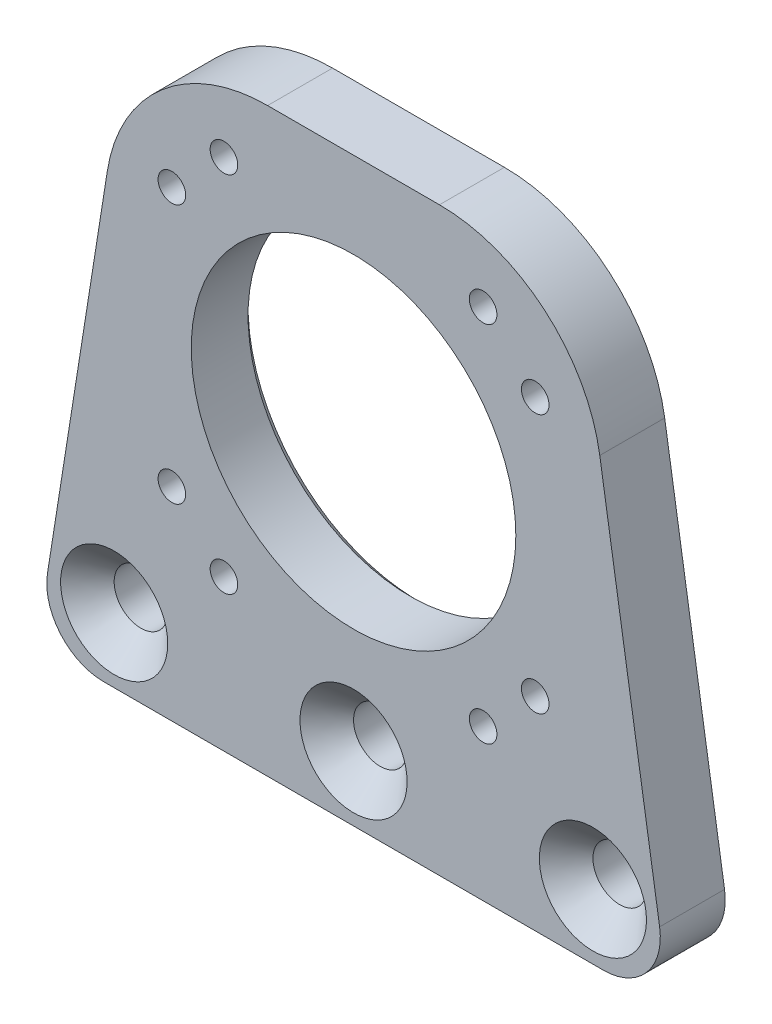
SolidWorks part; units mm, degrees
ref_plane "前视基准面" through (0, 0, 0) normal (0, 0, 1) x (1, 0, 0)
ref_plane "上视基准面" through (0, 0, 0) normal (0, 1, 0) x (1, 0, 0)
ref_plane "右视基准面" through (0, 0, 0) normal (1, 0, 0) x (0, 0, -1)
sketch "草图1" plane through (0, 0, 0) normal (0, 0, 1) x (1, 0, 0)
  line L0 (-37.7195, 14.8938) -> (-30.3438, 61.5147)
  line L1 (-37.7195, 14.8938) -> (-36.6269, 21.8) construction
  line L2 (0, 47.8) -> (0, 0) construction
  line L3 (-25, 72.8) -> (25, 72.8) construction
  line L4 (-25, 72.8) -> (-25, 22.8) construction
  line L5 (-25, 22.8) -> (25, 22.8) construction
  line L6 (25, 72.8) -> (25, 22.8) construction
  line L7 (-25, 72.8) -> (25, 22.8) construction
  line L8 (-25, 22.8) -> (25, 72.8) construction
  line L9 (-36.6269, 21.8) -> (36.6269, 21.8) construction
  line L10 (-10.5895, 78.3895) -> (10.5895, 78.3895)
  line L11 (37.7195, 14.8938) -> (30.3438, 61.5147)
  line L12 (-30.8055, 6.8) -> (30.8055, 6.8)
  line L13 (-15.9693, 70.1882) -> (0, 47.8) construction
  line L14 (0, 47.8) -> (-43.0568, 47.8) construction
  arc A0 (-30.3438, 61.5147) -> (-10.5895, 78.3895) centre (-10.5895, 58.3895) cw
  arc A1 (30.3438, 61.5147) -> (10.5895, 78.3895) centre (10.5895, 58.3895) ccw
  arc A2 (-37.7195, 14.8938) -> (-30.8055, 6.8) centre (-30.8055, 13.8) ccw
  arc A3 (37.7195, 14.8938) -> (30.8055, 6.8) centre (30.8055, 13.8) cw
  circle A4 centre (0, 47.8) radius 20
  circle A5 centre (0, 47.8) radius 27.5 construction
  circle A6 centre (-15.9693, 70.1882) radius 1.5
  circle A7 centre (-22.3882, 63.7693) radius 1.5
  circle A8 centre (-22.3882, 31.8307) radius 1.5
  circle A9 centre (-15.9693, 25.4118) radius 1.5
  circle A10 centre (15.9693, 25.4118) radius 1.5
  circle A11 centre (22.3882, 31.8307) radius 1.5
  circle A12 centre (22.3882, 63.7693) radius 1.5
  circle A13 centre (15.9693, 70.1882) radius 1.5
  circle A14 centre (-29.5, 14.8) radius 3
  circle A15 centre (0, 14.8) radius 3
  circle A16 centre (29.5, 14.8) radius 3
  point P5 (0, 47.8)
  point P22 (0, 78.3895)
  dimension "D3" = 20
  dimension "D4" = 40
  dimension "D5" = 55
  dimension "D7" = 3
  dimension "D8" = 6
  dimension "D1" = 50
  dimension "D2" = 1
  dimension "D6" = 54.5
extrude "凸台-拉伸1" add sketch "草图1" along normal blind 8
hole_wizard "打孔尺寸(%根据十字)槽沉头木螺钉的类型1" positions "草图2" profile "草图3" countersink size "M3" standard "GB"
sketch "草图2" plane through (0, 0, 0) normal (0, 0, -1) x (-1, 0, 0)
  point P0 (-22.3882, 63.7693)
  point P3 (-15.9693, 70.1882)
  point P6 (15.9693, 70.1882)
  point P9 (22.3882, 63.7693)
  point P12 (-22.3882, 31.8307)
  point P15 (-15.9693, 25.4118)
  point P18 (15.9693, 25.4118)
  point P21 (22.3882, 31.8307)
sketch "草图3" plane through (22.3882, 63.7693, 0) normal (1, 0, 0) x (0, 1, 0)
  line L0 (0, 0) -> (0, 9.1215)
  line L1 (0, 9.1215) -> (1.7, 8.1)
  line L2 (1.7, 8.1) -> (1.7, 1.6)
  line L3 (1.7, 1.6) -> (3.3, 0)
  line L5 (3.3, 0) -> (0, 0)
  line L6 (-1.7, 1.6) -> (-3.3, 0) construction
  line L10 (0, 9.1215) -> (-1.7, 8.1) construction
  line L11 (0, -6.35) -> (0, 107.95) construction
  dimension "孔直径" = 3.4
  dimension "孔深度" = 8.1
  dimension "近端锥形沉头孔直径" = 6.6
  dimension "近端锥形沉头孔角度" = 90
  dimension "导头角度" = 118
hole_wizard "打孔尺寸(%根据十字)槽沉头木螺钉的类型2" positions "草图4" profile "草图5" countersink size "M6" standard "GB"
sketch "草图4" plane through (0, 0, 8) normal (0, 0, 1) x (1, 0, 0)
  point P0 (29.5, 14.8)
  point P3 (0, 14.8)
  point P6 (-29.5, 14.8)
sketch "草图5" plane through (29.5, 14.8, 8) normal (1, 0, 0) x (0, -1, 0)
  line L0 (0, 0) -> (0, 10.0828)
  line L1 (0, 10.0828) -> (3.3, 8.1)
  line L2 (3.3, 8.1) -> (3.3, 3.3)
  line L3 (3.3, 3.3) -> (6.6, 0)
  line L5 (6.6, 0) -> (0, 0)
  line L6 (-3.3, 3.3) -> (-6.6, 0) construction
  line L10 (0, 10.0828) -> (-3.3, 8.1) construction
  line L11 (0, -6.35) -> (0, 107.95) construction
  dimension "孔直径" = 6.6
  dimension "孔深度" = 8.1
  dimension "近端锥形沉头孔直径" = 13.2
  dimension "近端锥形沉头孔角度" = 90
  dimension "导头角度" = 118
chamfer "倒角1" distance 1 angle 45 1 edges at (20, 47.8, 0)
